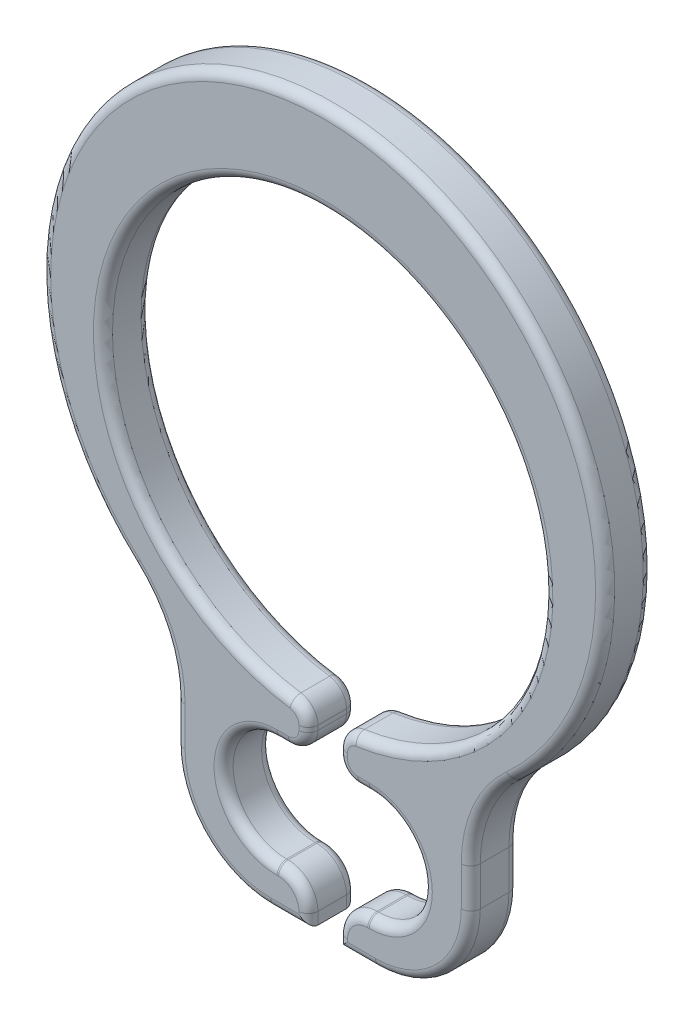
SolidWorks part; units mm, degrees
material "Plain Carbon Steel"
ref_plane "Front Plane" through (0, 0, 0) normal (0, 0, 1) x (1, 0, 0)
ref_plane "Top Plane" through (0, 0, 0) normal (0, 1, 0) x (1, 0, 0)
ref_plane "Right Plane" through (0, 0, 0) normal (1, 0, 0) x (0, 0, -1)
sketch "Sketch1" plane through (0, 0, 0) normal (0, 0, 1) x (1, 0, 0)
  line L0 (0, 6.05) -> (0, -6.05) construction
  line L1 (-0.88, -4.45) -> (0.88, -4.45) construction
  line L2 (-0.88, -3.85) -> (0.88, -3.85)
  line L3 (-0.88, -5.05) -> (0.88, -5.05)
  line L4 (1.48, -4.45) -> (2.48, -4.45) construction
  line L5 (0, -2.85) -> (0, -3.85) construction
  line L6 (0, 0) -> (2.1565, -2.1565) construction
  circle A0 centre (0, 0.85) radius 3.7
  arc A3 (-0.88, -3.85) -> (-0.88, -5.05) centre (-0.88, -4.45) ccw
  arc A4 (0.88, -5.05) -> (0.88, -3.85) centre (0.88, -4.45) ccw
  circle A5 centre (0, 1.3125) radius 4.7375 construction
  point P6 (0, 4.55)
  point P7 (0, -2.85)
  point P10 (0, -4.45)
  point P21 (-4.7375, 1.3125)
  point P22 (2.1565, -2.1565)
  point P28 (0, 6.05)
  dimension "Ring ID" = 7.4
  dimension "Band Width" = 1.5
  dimension "Tap Height" = 3.2
  dimension "Tap ID" = 1.2
  dimension "D3" = 1.6
  dimension "Tap Width Ref" = 4.96
  dimension "D1" = 0.4625
  dimension "D2" = 45
sketch "Sketch2" plane through (0, 0, 0) normal (0, 1, 0) x (0, 0, -1)
  line L0 (-0.4, 4.7375) -> (0.4, 4.7375) construction
  point P2 (0, 4.7375)
  dimension "Ring Thickness" = 0.8
sketch "Sketch3" plane through (0, 0, 0) normal (0, 0, 1) x (1, 0, 0)
  line L0 (-0.88, -5.05) -> (0.88, -5.05) construction
  line L1 (-0.88, -3.85) -> (0.88, -3.85) construction
  line L2 (-0.88, -5.05) -> (0.88, -5.05) construction
  line L3 (-0.88, -3.85) -> (0.88, -3.85) construction
  line L4 (2.48, -3.7922) -> (2.48, -4.45)
  line L5 (-0.88, -6.05) -> (0.88, -6.05)
  line L6 (-2.48, -3.7922) -> (-2.48, -4.45)
  line L7 (-1.48, -4.45) -> (-2.48, -4.45) construction
  line L8 (1.48, -4.45) -> (2.48, -4.45) construction
  line L10 (-0.774, -4.45) -> (0.774, -4.45) construction
  line L11 (0, 6.05) -> (0, -6.05) construction
  line L13 (0, -3.85) -> (0, -3.425) construction
  line L14 (0, -5.05) -> (0, -5.475) construction
  line L15 (-0.774, -3.55) -> (0.774, -3.55)
  line L16 (-0.774, -5.35) -> (0.774, -5.35)
  line L17 (-0.88, -4.45) -> (0.88, -4.45) construction
  arc A0 (-0.88, -3.85) -> (-0.88, -5.05) centre (-0.88, -4.45) ccw construction
  arc A1 (0.88, -5.05) -> (0.88, -3.85) centre (0.88, -4.45) ccw construction
  arc A2 (-0.88, -3.85) -> (-0.88, -5.05) centre (-0.88, -4.45) ccw construction
  arc A3 (0.88, -5.05) -> (0.88, -3.85) centre (0.88, -4.45) ccw construction
  circle A4 centre (0, 0.85) radius 3.7 construction
  circle A5 centre (0, 0.85) radius 3.7
  arc A6 (-3.1876, -2.1922) -> (3.1876, -2.1922) centre (0, 1.3125) cw
  arc A7 (-0.774, -3.55) -> (-0.774, -5.35) centre (-0.774, -4.45) ccw
  arc A8 (3.1876, -2.1922) -> (2.48, -3.7922) centre (4.6428, -3.7922) ccw
  arc A9 (2.48, -4.45) -> (0.88, -6.05) centre (0.88, -4.45) cw
  arc A10 (-3.1876, -2.1922) -> (-2.48, -3.7922) centre (-4.6428, -3.7922) cw
  arc A11 (-2.48, -4.45) -> (-0.88, -6.05) centre (-0.88, -4.45) ccw
  circle A12 centre (0, 1.3125) radius 4.7375 construction
  arc A13 (0.774, -5.35) -> (0.774, -3.55) centre (0.774, -4.45) ccw
  point P40 (0, -4.45)
  dimension "D1" = 1.6
  dimension "D2" = 1.6
  dimension "D3" = 1
  dimension "D4" = 1.8
  dimension "D5" = 3.348
extrude "Boss-Extrude1" add sketch "Sketch3" along normal mid plane 0.8
sketch "Sketch4" plane through (0, 0, 0) normal (0, 0, 1) x (1, 0, 0)
  line L0 (0, 0.85) -> (0, -6.05)
extrude "Cut-Extrude-Thin1" cut sketch "Sketch4" against normal through all both and the other way through all thin thin type mid plane wall 0.496
fillet "Fillet2" radius 0.5 2 edges at (0.248, -5.35, 0) (-0.248, -5.35, 0)
fillet "Fillet3" radius 0.3333 4 edges at (0.248, -3.55, 0) (0.248, -2.8417, 0) (-0.248, -3.55, 0) (-0.248, -2.8417, 0)
fillet "Fillet1" radius 0.16 52 edges at (0, 4.55, -0.4) (0.248, -5.95, -0.4) (0.564, -6.05, -0.4) (2.0114, -5.5814, -0.4) (2.48, -4.1211, -0.4) (2.6648, -2.9175, -0.4) (0, 6.05, -0.4) (-2.6648, -2.9175, -0.4) (-2.48, -4.1211, -0.4) (-2.0114, -5.5814, -0.4) (-0.564, -6.05, -0.4) (-0.248, -5.95, -0.4) (-2.0114, -5.5814, 0.4) (-2.48, -4.1211, 0.4) (-2.6648, -2.9175, 0.4) (0, 6.05, 0.4) (2.6648, -2.9175, 0.4) (2.48, -4.1211, 0.4) (2.0114, -5.5814, 0.4) (0.564, -6.05, 0.4) (0.248, -5.95, 0.4) (0, 4.55, 0.4) (-0.248, -5.95, 0.4) (-0.564, -6.05, 0.4) (0.6777, -3.55, -0.4) (1.674, -4.45, -0.4) (0.761, -5.35, -0.4) (-0.761, -5.35, -0.4) (-1.674, -4.45, -0.4) (-0.6777, -3.55, -0.4) (-0.6777, -3.55, 0.4) (-1.674, -4.45, 0.4) (-0.761, -5.35, 0.4) (0.761, -5.35, 0.4) (1.674, -4.45, 0.4) (0.6777, -3.55, 0.4) (0.3944, -5.4964, -0.4) (-0.3944, -5.4964, -0.4) (-0.3456, -3.4524, -0.4) (-0.248, -3.1789, -0.4) (-0.3292, -2.9232, -0.4) (0.3292, -2.9232, -0.4) (0.248, -3.1789, -0.4) (0.3456, -3.4524, -0.4) (0.3292, -2.9232, 0.4) (-0.3292, -2.9232, 0.4) (-0.248, -3.1789, 0.4) (-0.3456, -3.4524, 0.4) (-0.3944, -5.4964, 0.4) (0.3944, -5.4964, 0.4) (0.3456, -3.4524, 0.4) (0.248, -3.1789, 0.4)
equation "\"D3@Sketch1\"=\"Tap Height@Sketch1\"*0.5"
equation "\"D1@Boss-Extrude1\"=\"Ring Thickness@Sketch2\""
equation "\"D1@Sketch1\"=\"Ring ID@Sketch1\"*0.0625"
equation "\"D5@Cut-Extrude-Thin1\"=\"Tap Width Ref@Sketch1\"/10"
equation "\"D4@Sketch3\"=\"Tap ID@Sketch1\"*1.5"
equation "\"D1@Fillet2\"=\"D3@Sketch3\"*0.5"
equation "\"D1@Fillet3\"=\"D1@Fillet2\"/1.5"
equation "\"D1@Fillet1\"=\"Ring Thickness@Sketch2\"*.2"
equation "\"D2@Sketch3\"=\"Tap Height@Sketch1\"*0.5"
equation "\"D1@Sketch3\"=\"Tap Height@Sketch1\"*0.5"
equation "\"Tap Width Ref@Sketch1\"=\"Tap Height@Sketch1\"*1.55"
equation "\"D5@Sketch3\"=\"Tap Width Ref@Sketch1\"*.675"
